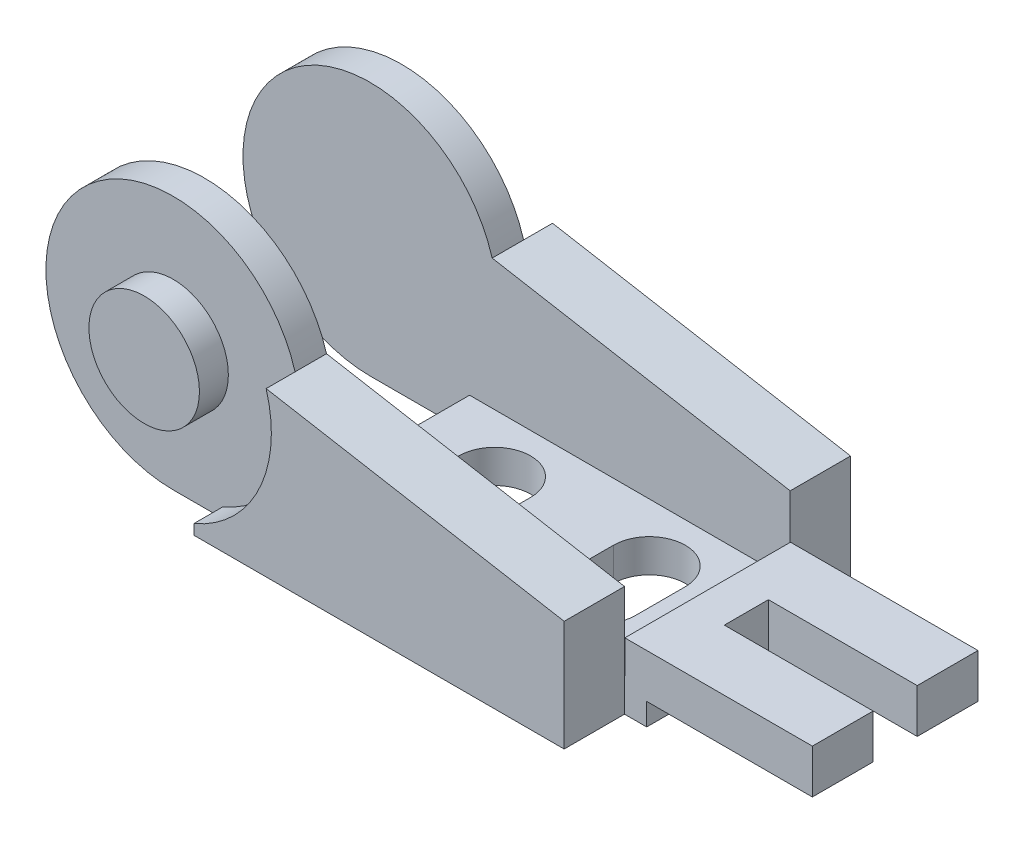
SolidWorks part; units mm, degrees
ref_plane "Front Plane" through (0, 0, 0) normal (0, 0, 1) x (1, 0, 0)
ref_plane "Top Plane" through (0, 0, 0) normal (0, 1, 0) x (1, 0, 0)
ref_plane "Right Plane" through (0, 0, 0) normal (1, 0, 0) x (0, 0, -1)
sketch "Sketch1" plane through (0, 0, 0) normal (0, 0, 1) x (1, 0, 0)
  line L0 (0, -11.5062) -> (37.9984, -11.5062)
  line L1 (37.9984, -11.5062) -> (37.9984, -1.4986)
  line L2 (37.9984, -1.4986) -> (11.036, 3.2556)
  line L3 (4.4952, -10.5918) -> (4.4952, -11.5062)
  line L4 (37.9984, -11.5062) -> (40.005, -11.5062)
  line L5 (40.005, -11.5062) -> (40.005, -9.4996)
  line L6 (40.005, -9.4996) -> (54.991, -9.4996)
  line L7 (54.991, -9.4996) -> (54.991, -5.5118)
  line L8 (54.991, -5.5118) -> (37.9984, -5.5118)
  circle A0 centre (0, 0) radius 5
  arc A1 (4.4952, -10.5918) -> (0, -11.5062) centre (0, 0) ccw
  dimension "D1" = 10
  dimension "D2" = 23.0124
  dimension "D3" = 10
  dimension "D4" = 10.0076
  dimension "D5" = 37.9984
  dimension "D6" = 0.9144
  dimension "D7" = 2.0066
  dimension "D8" = 3.9878
  dimension "D9" = 54.991
sketch "Sketch2" plane through (0, 0, 0) normal (0, 0, 1) x (1, 0, 0)
  line L0 (37.9984, -11.5062) -> (37.9984, -1.4986) construction
  line L1 (0, -11.5062) -> (37.9984, -11.5062) construction
  line L2 (37.9984, -1.4986) -> (11.036, 3.2556) construction
  line L3 (37.9984, -11.5062) -> (37.9984, -1.4986)
  line L4 (0, -11.5062) -> (37.9984, -11.5062)
  line L5 (37.9984, -1.4986) -> (11.036, 3.2556)
  arc A0 (4.4952, -10.5918) -> (0, -11.5062) centre (0, 0) ccw construction
  arc A1 (11.036, 3.2556) -> (0, -11.5062) centre (0, 0) ccw
extrude "Extrude1" add sketch "Sketch2" along normal mid plane 25.908
sketch "Sketch3" plane through (0, 0, 12.954) normal (0, 0, 1) x (1, 0, 0)
  line L0 (0, -11.5062) -> (37.9984, -11.5062) construction
  line L1 (0, -11.5062) -> (4.4952, -11.5062)
  line L2 (4.4952, -10.5918) -> (4.4952, -11.5062) construction
  line L3 (4.4952, -10.5918) -> (4.4952, -11.5062)
  arc A0 (4.4952, -10.5918) -> (0, -11.5062) centre (0, 0) ccw construction
  circle A1 centre (0, 0) radius 5 construction
  arc A2 (4.4952, -10.5918) -> (0, -11.5062) centre (0, 0) ccw
  circle A3 centre (0, 0) radius 5
extrude "Cut-Extrude1" cut sketch "Sketch3" against normal blind 2.6162
mirror "Mirror1" about plane through (0, 0, 0) normal (0, 0, 1) of "Cut-Extrude1"
sketch "Sketch4" plane through (0, 0, 0) normal (0, 0, 1) x (1, 0, 0)
  line L1 (8.9916, -8.509) -> (37.9984, -8.509)
  line L2 (8.9916, -8.509) -> (8.9916, -11.5062)
  line L3 (37.9984, -11.5062) -> (37.9984, -1.4986)
  line L4 (37.9984, -1.4986) -> (11.036, 3.2556)
  line L5 (0, -11.5062) -> (37.9984, -11.5062)
  line L6 (37.9984, -8.509) -> (37.9984, -1.4986)
  line L7 (37.9984, -1.4986) -> (11.036, 3.2556)
  line L8 (0, -11.5062) -> (8.9916, -11.5062)
  arc A1 (11.036, 3.2556) -> (0, -11.5062) centre (0, 0) ccw
  arc A2 (11.036, 3.2556) -> (0, -11.5062) centre (0, 0) ccw
  dimension "D2" = 29.0068
  dimension "D3" = 2.9972
  dimension "D1" = 0
extrude "Cut-Extrude2" cut sketch "Sketch4" against normal mid plane 14.986
sketch "Sketch5" plane through (0, 0, 0) normal (0, 0, 1) x (1, 0, 0)
  line L0 (54.991, -5.5118) -> (37.9984, -5.5118) construction
  line L1 (54.991, -9.4996) -> (54.991, -5.5118) construction
  line L2 (40.005, -9.4996) -> (54.991, -9.4996) construction
  line L3 (40.005, -11.5062) -> (40.005, -9.4996) construction
  line L4 (37.9984, -11.5062) -> (37.9984, -1.4986) construction
  line L5 (37.9984, -11.5062) -> (40.005, -11.5062) construction
  line L6 (54.991, -5.5118) -> (38.0238, -5.5118)
  line L7 (54.991, -9.4996) -> (54.991, -5.5118)
  line L8 (40.005, -9.4996) -> (54.991, -9.4996)
  line L9 (40.005, -11.5062) -> (40.005, -9.4996)
  line L10 (37.9984, -11.5062) -> (37.9984, -8.509)
  line L11 (37.9984, -11.5062) -> (40.005, -11.5062)
  line L12 (8.9916, -8.509) -> (37.9984, -8.509) construction
  line L13 (37.9984, -8.509) -> (38.0238, -8.509)
  line L14 (38.0238, -8.509) -> (38.0238, -5.5118)
  dimension "D1" = 0.0254
extrude "Extrude2" add sketch "Sketch5" against normal up to surface and the other way up to surface up to face at (15.0471, -4.5431, -7.493) other way up to face at (15.0471, -4.5431, 7.493)
sketch "Sketch7" plane through (0, -5.5118, 0) normal (0, 1, 0) x (1, 0, 0)
  line L0 (54.991, 7.493) -> (54.991, -7.493) construction
  line L1 (41.529, 1.9939) -> (54.991, 1.9939)
  line L2 (41.529, 1.9939) -> (41.529, -1.9939)
  line L3 (41.529, -1.9939) -> (54.991, -1.9939)
  line L4 (54.991, 1.9939) -> (54.991, -1.9939)
  line L5 (38.0238, 7.493) -> (38.0238, -7.493) construction
  line L6 (0, 0) -> (41.529, 0) construction
  dimension "D1" = 3.5052
  dimension "D2" = 3.9878
extrude "Cut-Extrude3" cut sketch "Sketch7" against normal through all
sketch "Sketch8" plane through (0, -8.509, 0) normal (0, 1, 0) x (1, 0, 0)
  line L0 (19.7612, 2.2479) -> (19.7612, -2.2479)
  line L2 (13.2588, 2.2479) -> (13.2588, -2.2479)
  line L3 (16.51, 0) -> (30.5054, 0) construction
  line L4 (23.5077, 0) -> (23.5077, 4.5528) construction
  line L5 (33.7566, 2.2479) -> (33.7566, -2.2479)
  line L6 (27.2542, 2.2479) -> (27.2542, -2.2479)
  line L7 (16.51, -2.2479) -> (16.51, 2.2479) construction
  line L8 (13.2588, 0) -> (8.9916, 0) construction
  line L9 (33.7566, 0) -> (38.0238, 0) construction
  line L10 (38.0238, 7.493) -> (38.0238, -7.493) construction
  line L11 (8.9916, 7.493) -> (8.9916, -7.493) construction
  arc A0 (19.7612, 2.2479) -> (13.2588, 2.2479) centre (16.51, 2.2479) ccw
  arc A1 (13.2588, -2.2479) -> (19.7612, -2.2479) centre (16.51, -2.2479) ccw
  arc A2 (33.7566, -2.2479) -> (27.2542, -2.2479) centre (30.5054, -2.2479) cw
  arc A3 (27.2542, 2.2479) -> (33.7566, 2.2479) centre (30.5054, 2.2479) cw
  dimension "D1" = 3.2512
  dimension "D2" = 4.4958
  dimension "D3" = 13.9954
extrude "Cut-Extrude4" cut sketch "Sketch8" against normal through all
ref_plane "Plane1" through (-19.05, 0, 0) normal (1, 0, 0) x (0, 0, -1)
mirror "Mirror3" [suppressed] about plane through (-19.05, 0, 0) normal (1, 0, 0)
sketch "Sketch9" [suppressed] plane through (0, 0, 12.954) normal (0, 0, 1) x (1, 0, 0)
  circle A1 centre (-38.1, 0) radius 5
  circle A2 centre (-38.1, 0) radius 5
  dimension "D1" = 0
sketch "Sketch10" [suppressed] plane through (0, 0, 10.3378) normal (0, 0, 1) x (1, 0, 0)
  line L2 (-42.5952, -10.5918) -> (-42.5952, -11.5062)
  line L3 (-42.5952, -11.5062) -> (-38.1, -11.5062)
  line L4 (-42.5952, -10.5918) -> (-42.5952, -11.5062)
  line L5 (-42.5952, -11.5062) -> (-38.1, -11.5062)
  arc A2 (-49.136, 3.2556) -> (-42.5952, -10.5918) centre (-38.1, 0) ccw
  arc A3 (-38.1, -11.5062) -> (-49.136, 3.2556) centre (-38.1, 0) ccw
  arc A4 (-49.136, 3.2556) -> (-42.5952, -10.5918) centre (-38.1, 0) ccw
  arc A5 (-38.1, -11.5062) -> (-49.136, 3.2556) centre (-38.1, 0) ccw
  dimension "D1" = 0
extrude "Extrude3" [suppressed] add sketch "Sketch10" along normal up to surface (2.6162 mm away)
sketch "Sketch11" [suppressed] plane through (0, 0, -10.3378) normal (0, 0, -1) x (-1, 0, 0)
  line L2 (38.1, -11.5062) -> (42.5952, -11.5062)
  line L3 (42.5952, -11.5062) -> (42.5952, -10.5918)
  line L4 (38.1, -11.5062) -> (42.5952, -11.5062)
  line L5 (42.5952, -11.5062) -> (42.5952, -10.5918)
  arc A2 (42.5952, -10.5918) -> (49.136, 3.2556) centre (38.1, 0) ccw
  arc A3 (49.136, 3.2556) -> (38.1, -11.5062) centre (38.1, 0) ccw
  arc A4 (42.5952, -10.5918) -> (49.136, 3.2556) centre (38.1, 0) ccw
  arc A5 (49.136, 3.2556) -> (38.1, -11.5062) centre (38.1, 0) ccw
  dimension "D1" = 0
extrude "Extrude4" [suppressed] add sketch "Sketch11" along normal up to surface (2.6162 mm away)
extrude "Cut-Extrude5" [suppressed] cut sketch "Sketch9" against normal through all
sketch "Sketch12" [suppressed] plane through (0, 0, 0) normal (0, 0, 1) x (1, 0, 0)
  line L0 (-76.0984, -1.4986) -> (-49.136, 3.2556) construction
  line L1 (-76.0984, -1.4986) -> (-28.843, 6.8338) construction
  circle A0 centre (-38.1, 0) radius 11.5062
  arc A1 (-38.1, -11.5062) -> (-49.136, 3.2556) centre (-38.1, 0) ccw construction
  arc A2 (-38.1, -11.5062) -> (-49.136, 3.2556) centre (-38.1, 0) ccw construction
extrude "Cut-Extrude6" [suppressed] cut sketch "Sketch12" along normal up to surface and the other way up to surface
